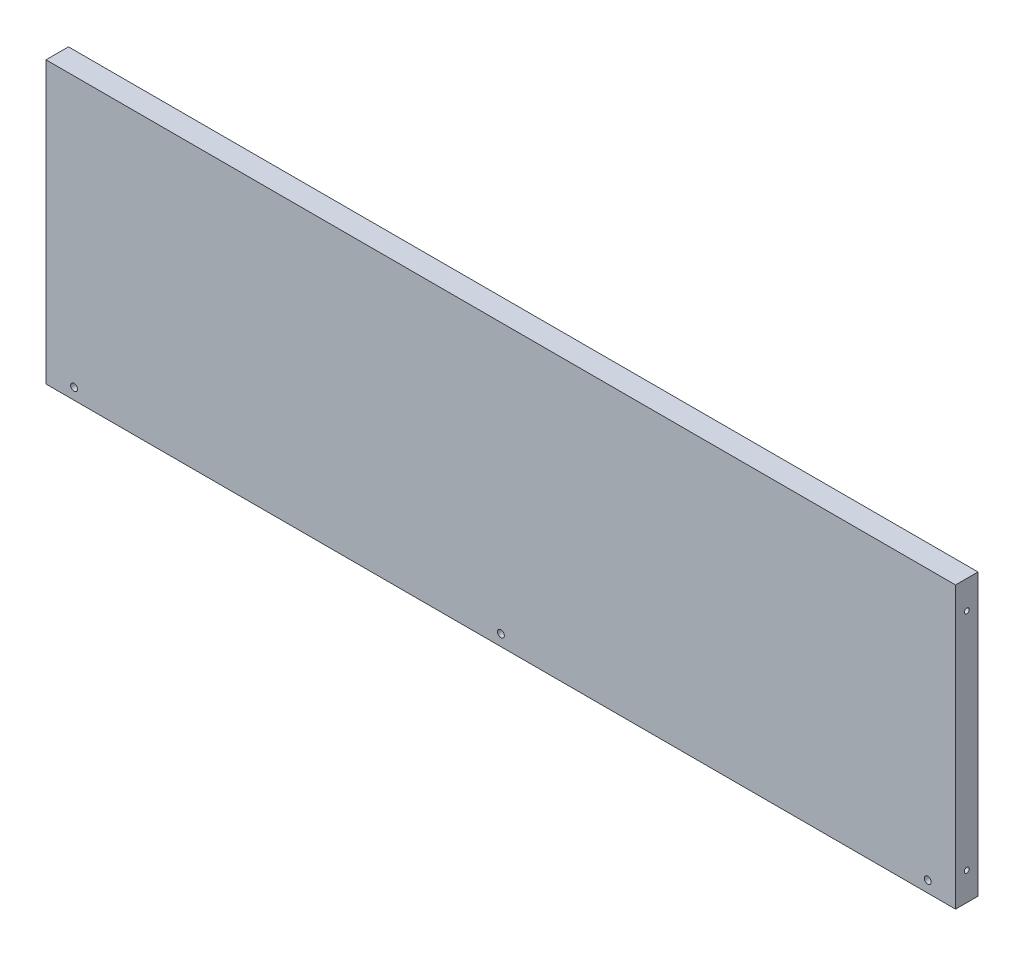
SolidWorks part; units mm, degrees
ref_plane "Front Plane" through (0, 0, 0) normal (0, 0, 1) x (1, 0, 0)
ref_plane "Top Plane" through (0, 0, 0) normal (0, 1, 0) x (1, 0, 0)
ref_plane "Right Plane" through (0, 0, 0) normal (1, 0, 0) x (0, 0, -1)
sketch "Sketch1" plane through (0, 0, 0) normal (0, 0, 1) x (1, 0, 0)
  line L1 (0, 0) -> (324, 0)
  line L2 (0, 0) -> (0, 100)
  line L3 (0, 100) -> (324, 100)
  line L4 (324, 0) -> (324, 100)
  dimension "D1" = 100
  dimension "D2" = 324
extrude "Boss-Extrude1" add sketch "Sketch1" along normal blind 8
hole_wizard "CBORE for #2 Socket Head Cap Screw1" positions "Sketch2" profile "Sketch3" counterbore size "#2" standard "ANSI Inch" end condition through all
sketch "Sketch2" plane through (0, 0, 0) normal (0, 0, -1) x (-1, 0, 0)
  line L0 (-306, 100) -> (-306, 0)
  line L1 (-324, 100) -> (0, 100) construction
  line L2 (0, 0) -> (-324, 0) construction
  line L5 (-8, 100) -> (-8, 0)
  point P2 (-314, 4)
  point P4 (-10, 4)
  point P27 (-162, 4)
  point P32 (-162, 0)
  dimension "D1" = 152
  dimension "D2" = 152
  dimension "D3" = 4
  dimension "D4" = 4
  dimension "D7" = 0
  dimension "D8" = 4
sketch "Sketch3" plane through (314, 4, 0) normal (1, 0, 0) x (0, 1, 0)
  line L0 (0, 0) -> (0, 8)
  line L1 (0, 8) -> (1.2192, 8)
  line L3 (1.2192, 8) -> (1.2192, 2.1844)
  line L4 (1.2192, 2.1844) -> (2.3812, 2.1844)
  line L5 (2.3812, 2.1844) -> (2.3812, 0)
  line L7 (2.3812, 0) -> (0, 0)
  line L11 (0, -6.35) -> (0, 107.95) construction
  dimension "Thru Hole Dia." = 2.4384
  dimension "Thru Hole Depth" = 8
  dimension "C'Bore Dia." = 4.7625
  dimension "C'Bore Depth" = 2.1844
hole_wizard "#2-56 Tapped Hole1" positions "Sketch7" profile "Sketch6" tap size "#2-56" standard "ANSI Inch"
sketch "Sketch7" plane through (324, 0, 0) normal (1, 0, 0) x (0, 0, -1)
  line L0 (-8, 100) -> (0, 100) construction
  line L1 (-8, 0) -> (0, 0) construction
  point P0 (-4, 90)
  point P2 (-4, 10)
  dimension "D1" = 10
  dimension "D2" = 10
sketch "Sketch6" plane through (324, 90, 4) normal (0, 1, 0) x (0, 0, -1)
  line L0 (0, 0) -> (0, 15.5342)
  line L1 (0, 15.5342) -> (0.889, 15)
  line L2 (0.889, 15) -> (0.889, 0)
  line L5 (0.889, 0) -> (0, 0)
  line L10 (0, 15.5342) -> (-0.889, 15) construction
  line L11 (0, -6.35) -> (0, 107.95) construction
  dimension "Tap Drill Dia." = 1.778
  dimension "Tap Drill Depth" = 15
  dimension "Drill Angle" = 118
cosmetic thread "Hole Thread1" parameters "D1"=12, "D2"=2.1844
cosmetic thread "Hole Thread2" parameters "D1"=12, "D2"=2.1844
hole_wizard "#2-56 Tapped Hole2" positions "Sketch8" profile "Sketch9" tap size "#2-56" standard "ANSI Inch"
sketch "Sketch8" plane through (0, 0, 0) normal (-1, 0, 0) x (0, 0, 1)
  line L0 (8, 100) -> (0, 100) construction
  line L2 (8, 0) -> (0, 0) construction
  point P0 (4, 90)
  point P2 (4, 10)
  dimension "D1" = 10
  dimension "D2" = 10
sketch "Sketch9" plane through (0, 90, 4) normal (0, 1, 0) x (0, 0, 1)
  line L0 (0, 0) -> (0, 15.5342)
  line L1 (0, 15.5342) -> (0.889, 15)
  line L2 (0.889, 15) -> (0.889, 0)
  line L5 (0.889, 0) -> (0, 0)
  line L10 (0, 15.5342) -> (-0.889, 15) construction
  line L11 (0, -6.35) -> (0, 107.95) construction
  dimension "Tap Drill Dia." = 1.778
  dimension "Tap Drill Depth" = 15
  dimension "Drill Angle" = 118
cosmetic thread "Hole Thread3" parameters "D1"=12, "D2"=2.1844
cosmetic thread "Hole Thread4" parameters "D1"=12, "D2"=2.1844
sketch "Sketch10" plane through (324, 0, 0) normal (1, 0, 0) x (0, 0, -1)
  line L1 (-8, 100) -> (0, 100)
  line L2 (-8, 100) -> (-8, 0)
  line L3 (-8, 0) -> (0, 0)
  line L4 (0, 100) -> (0, 0)
extrude "Cut-Extrude1" cut sketch "Sketch10" against normal blind 0.1
sketch "Sketch11" plane through (0, 0, 0) normal (-1, 0, 0) x (0, 0, 1)
  line L1 (0, 100) -> (8, 100)
  line L2 (0, 100) -> (0, 0)
  line L3 (0, 0) -> (8, 0)
  line L4 (8, 100) -> (8, 0)
